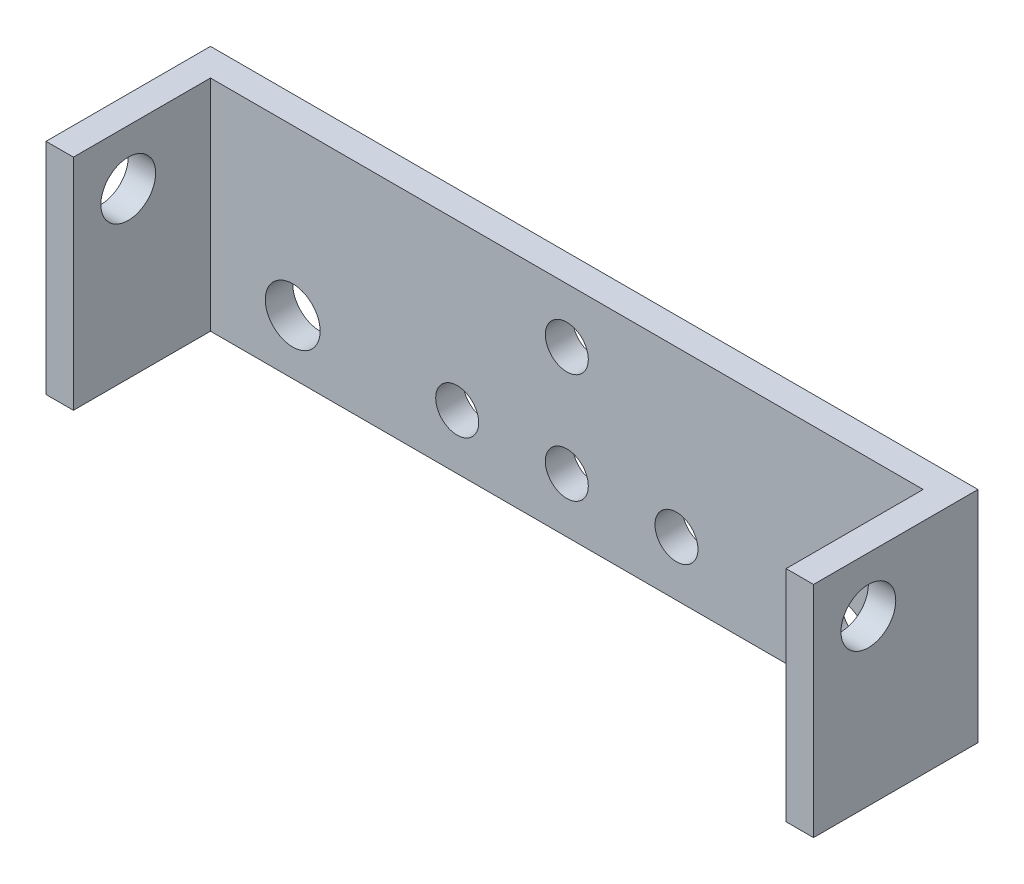
SolidWorks part; units mm, degrees
material "6061-T6 (SS)"
ref_plane "Front Plane" through (0, 0, 0) normal (0, 0, 1) x (1, 0, 0)
ref_plane "Top Plane" through (0, 0, 0) normal (0, 1, 0) x (1, 0, 0)
ref_plane "Right Plane" through (0, 0, 0) normal (1, 0, 0) x (0, 0, -1)
sketch "Sketch1" plane through (0, 0, 0) normal (0, 1, 0) x (1, 0, 0)
  line L0 (0, 0) -> (0, 19.05)
  line L1 (0, 19.05) -> (88.9, 19.05)
  line L2 (88.9, 19.05) -> (88.9, 0)
  line L3 (88.9, 0) -> (85.725, 0)
  line L4 (85.725, 0) -> (85.725, 15.875)
  line L5 (85.725, 15.875) -> (3.175, 15.875)
  line L6 (3.175, 15.875) -> (3.175, 0)
  line L7 (3.175, 0) -> (0, 0)
  dimension "D1" = 3.175
  dimension "D2" = 3.175
  dimension "D3" = 3.175
  dimension "D4" = 19.05
  dimension "D5" = 88.9
extrude "Boss-Extrude1" add sketch "Sketch1" along normal blind 25.4
sketch "Sketch2" plane through (88.9, 0, 0) normal (1, 0, 0) x (0, 0, -1)
  line L1 (0, 70.1036) -> (0, 49.1287) construction
  line L2 (19.05, 25.4) -> (19.05, 0) construction
  line L3 (0, 25.4) -> (19.05, 25.4) construction
  circle A0 centre (6.35, 19.05) radius 3.175
  circle A1 centre (6.35, 19.05) radius 6.35 construction
  dimension "D1" = 6.35
  dimension "D2" = 12.7
  dimension "D3" = 19.05
  dimension "D4" = 6.35
extrude "Cut-Extrude1" cut sketch "Sketch2" against normal through all
sketch "Sketch3" plane through (0, 0, -15.875) normal (0, 0, 1) x (1, 0, 0)
  line L0 (3.175, 25.4) -> (85.725, 25.4) construction
  line L1 (12.7, 6.35) -> (76.2, 6.35) construction
  line L2 (12.7, 6.35) -> (12.7, 26.2966) construction
  line L3 (12.7, 26.2966) -> (76.2, 26.2966) construction
  line L4 (76.2, 6.35) -> (76.2, 26.2966) construction
  circle A0 centre (12.7, 6.35) radius 3.175
  circle A1 centre (76.2, 6.35) radius 3.175
  point P8 (44.45, 25.4)
  point P9 (44.45, 6.35)
  dimension "D1" = 6.35
  dimension "D2" = 63.5
  dimension "D3" = 19.05
extrude "Cut-Extrude2" cut sketch "Sketch3" against normal through all both and the other way through all
sketch "Sketch4" plane through (0, 0, -15.875) normal (0, 0, 1) x (1, 0, 0)
  line L0 (44.45, 25.4) -> (44.45, 0) construction
  line L1 (3.175, 25.4) -> (85.725, 25.4) construction
  line L2 (3.175, 0) -> (85.725, 0) construction
  line L3 (54.61, 25.4) -> (54.61, 0) construction
  circle A0 centre (44.45, 19.05) radius 2.4892
  circle A1 centre (44.45, 6.35) radius 2.4892
  dimension "D2" = 4.9784
  dimension "D3" = 6.35
  dimension "D4" = 6.35
  dimension "D1" = 10.16
extrude "Cut-Extrude3" cut sketch "Sketch4" against normal through all
sketch "Sketch5" plane through (0, 0, -19.05) normal (0, 0, -1) x (-1, 0, 0)
  line L0 (-44.45, 0) -> (-44.45, 25.4) construction
  line L1 (-88.9, 0) -> (0, 0) construction
  line L2 (-88.9, 25.4) -> (0, 25.4) construction
  line L3 (-57.15, 6.35) -> (-31.75, 6.35) construction
  circle A0 centre (-31.75, 6.35) radius 2.4892
  circle A1 centre (-57.15, 6.35) radius 2.4892
  circle A2 centre (-44.45, 6.35) radius 2.4892 construction
  point P16 (-44.45, 6.35)
  dimension "D1" = 12.7
extrude "Cut-Extrude4" cut sketch "Sketch5" against normal through all
